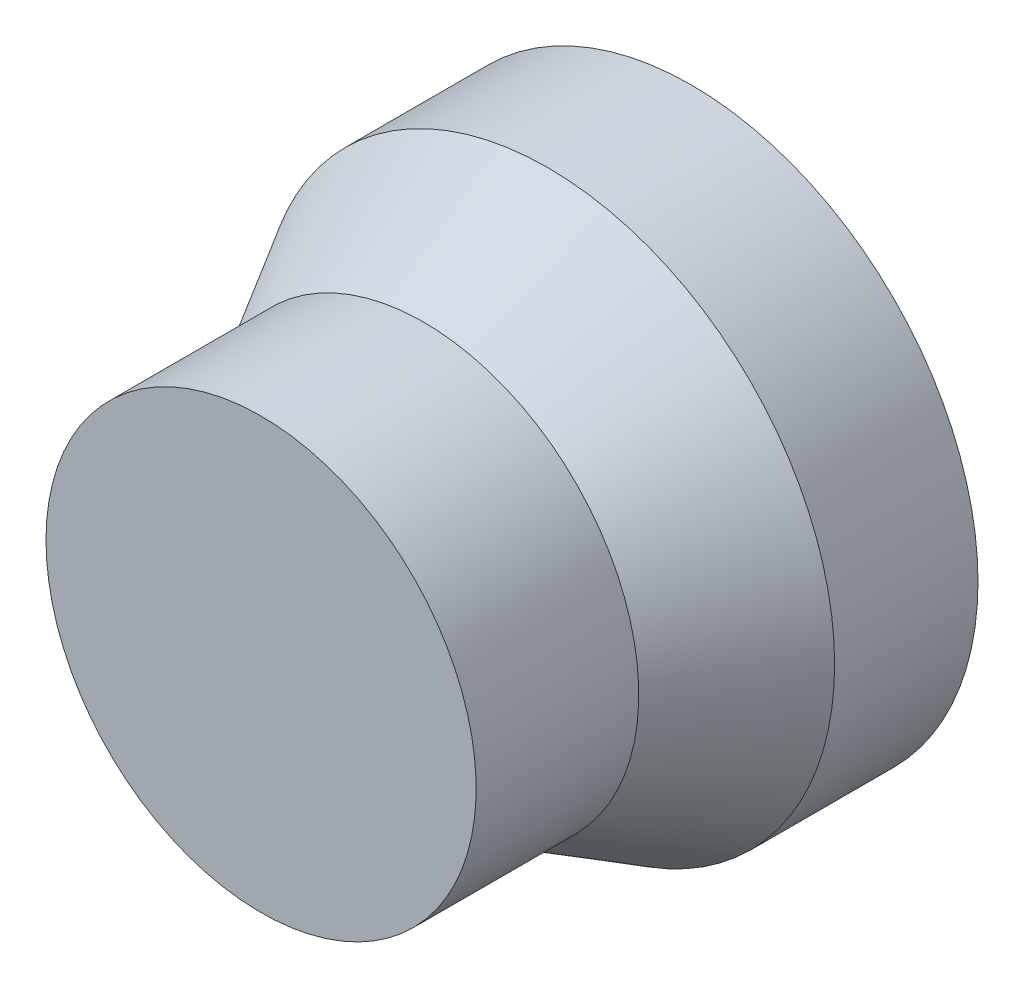
SolidWorks part; units mm, degrees
ref_plane "Front Plane" through (0, 0, 0) normal (0, 0, 1) x (1, 0, 0)
ref_plane "Top Plane" through (0, 0, 0) normal (0, 1, 0) x (1, 0, 0)
ref_plane "Right Plane" through (0, 0, 0) normal (1, 0, 0) x (0, 0, -1)
sketch "Sketch1" plane through (0, 0, 0) normal (0, 1, 0) x (1, 0, 0)
  line L0 (0, 165.5738) -> (0, -211.4754) construction
  line L1 (0, -150) -> (75, -150)
  line L2 (75, -150) -> (75, -93.3013)
  line L3 (75, -93.3013) -> (100, -50)
  line L4 (100, -50) -> (100, 0)
  line L5 (100, 0) -> (0, 0)
  line L6 (0, 0) -> (0, -150)
  dimension "D1" = 75
  dimension "D2" = 100
  dimension "D3" = 150
  dimension "D4" = 50
  dimension "D5" = 30
revolve "Revolve1" add sketch "Sketch1" angle 360 about L0
equation "\"base_link_diameter\"=75"
equation "\"base_link_length\"=150"
equation "\"D1\"= \"base_link_length\""
equation "\"link2_diameter\"=150"
equation "\"link2_length\"=300"
equation "\"link3_diameter\"=150"
equation "\"link3_length\"=150"
equation "\"link4_diameter\"=150"
equation "\"link4_length\"=150"
equation "\"link5_diameter\"=150"
equation "\"link5_length\"=200"
equation "\"end_effector_diameter\"=150"
equation "\"end_effector_length\"=150"
equation "\"base_link_diameterA\"=200"
equation "\"base_link_diameterB\"=150"
equation "\"D1@Sketch1\"=\"base_link_diameterB\"/2"
equation "\"D2@Sketch1\"=\"base_link_diameterA\"/2"
equation "\"D3@Sketch1\"=\"base_link_length\""
equation "\"base_link_lengthA\"=50"
equation "\"D4@Sketch1\"=\"base_link_lengthA\""
equation "\"link1_diameter\"=150"
equation "\"link1_length\"=150"
